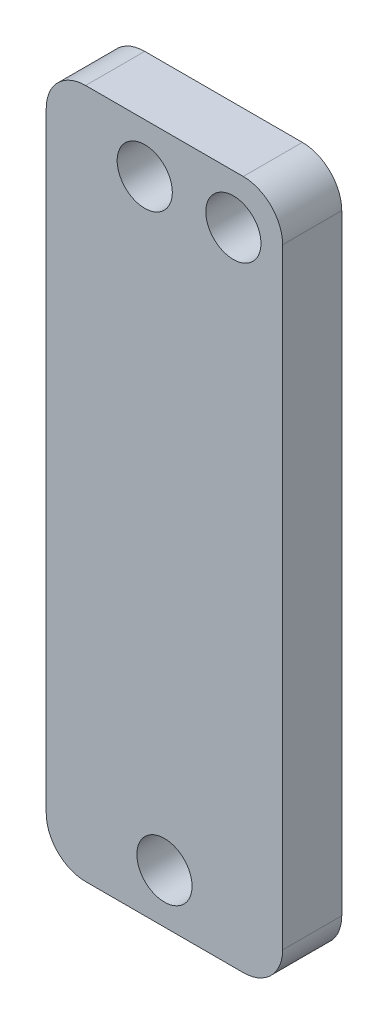
SolidWorks part; units mm, degrees
ref_plane "Plan de face" through (0, 0, 0) normal (0, 0, 1) x (1, 0, 0)
ref_plane "Plan de dessus" through (0, 0, 0) normal (0, 1, 0) x (1, 0, 0)
ref_plane "Plan de droite" through (0, 0, 0) normal (1, 0, 0) x (0, 0, -1)
sketch "Esquisse1" plane through (0, 0, 0) normal (0, 0, 1) x (1, 0, 0)
  line L1 (6, -17.5) -> (-6, -17.5)
  line L2 (6, -17.5) -> (6, 17.5)
  line L3 (6, 17.5) -> (-6, 17.5)
  line L4 (-6, -17.5) -> (-6, 17.5)
  line L5 (6, -17.5) -> (-6, 17.5) construction
  line L6 (6, 17.5) -> (-6, -17.5) construction
  circle A0 centre (-1, 15) radius 1.4
  circle A1 centre (0, -15) radius 1.4
  point P0 (0, 0)
  point P14 (0, -17.5)
  dimension "D5" = 2.8
  dimension "D1" = 12
  dimension "D2" = 35
  dimension "D3" = 2.5
  dimension "D4" = 2.5
  dimension "D6" = 5
extrude "Boss.-Extru.1" add sketch "Esquisse1" along normal blind 3
sketch "Esquisse2" plane through (0, 0, 0) normal (0, 0, -1) x (-1, 0, 0)
  line L0 (-6, 17.5) -> (6, 17.5) construction
  line L1 (-6, -17.5) -> (-6, 17.5) construction
  circle A0 centre (-3.5, 15) radius 1.4
  dimension "D1" = 2.8
  dimension "D2" = 2.5
  dimension "D3" = 2.5
extrude "Enlèv. mat.-Extru.1" cut sketch "Esquisse2" against normal through all
fillet "Congé1" radius 2 4 edges at (-6, -17.5, 1.5) (6, -17.5, 1.5) (-6, 17.5, 1.5) (6, 17.5, 1.5)
